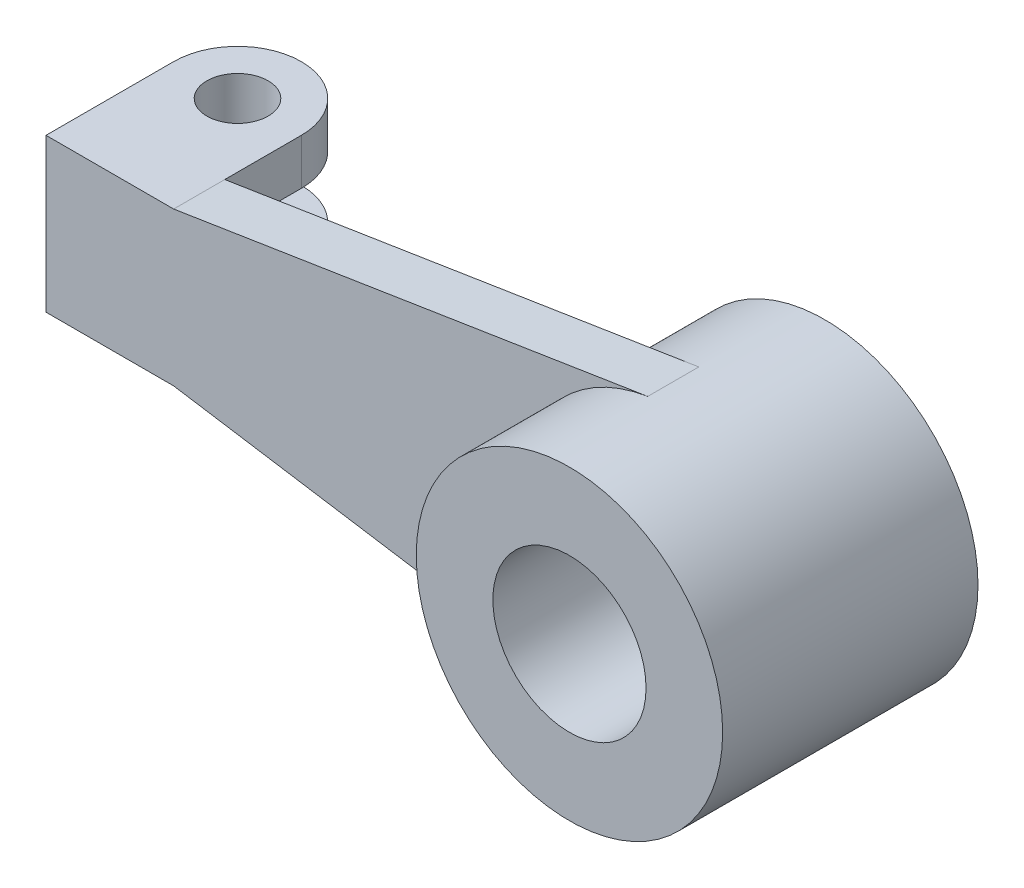
SolidWorks part; units mm, degrees
ref_plane "Front Plane" through (0, 0, 0) normal (0, 0, 1) x (1, 0, 0)
ref_plane "Top Plane" through (0, 0, 0) normal (0, 1, 0) x (1, 0, 0)
ref_plane "Right Plane" through (0, 0, 0) normal (1, 0, 0) x (0, 0, -1)
sketch "Sketch1" plane through (0, 0, 0) normal (0, 0, 1) x (1, 0, 0)
  circle A0 centre (0, 0) radius 30
  circle A1 centre (0, 0) radius 15
  dimension "D1" = 60
  dimension "D2" = 30
extrude "Boss-Extrude1" add sketch "Sketch1" along normal mid plane 50
sketch "Sketch3" plane through (0, 0, 0) normal (0, 0, 1) x (1, 0, 0)
  line L0 (0, 0) -> (-122.5, 0) construction
  line L1 (-122.5, -15) -> (-122.5, 15)
  line L2 (-122.5, 15) -> (-97.5, 15)
  line L3 (-97.5, 15) -> (-4.6717, 29.634)
  line L4 (-122.5, -15) -> (-97.5, -15)
  line L5 (-97.5, -15) -> (-4.6717, -29.634)
  circle A0 centre (0, 0) radius 30 construction
  arc A1 (-4.6717, 29.634) -> (-4.6717, -29.634) centre (0, 0) ccw
  dimension "D1" = 15
  dimension "D2" = 122.5
  dimension "D3" = 25
extrude "Boss-Extrude2" add sketch "Sketch3" along normal mid plane 10 contours A1 L5 L4 L1 L2 L3
sketch "Sketch6" plane through (-4.6717, 29.634, 0) normal (-0.1557, 0.9878, 0) x (0.9878, 0.1557, 0)
sketch "Sketch8" plane through (0, 15, 0) normal (0, 1, 0) x (1, 0, 0)
  line L0 (-122.5, 5) -> (-122.5, 20)
  line L1 (-97.5, 5) -> (-97.5, 20)
  line L2 (-122.5, 5) -> (-97.5, 5)
  line L3 (-122.5, -5) -> (-97.5, -5) construction
  arc A0 (-122.5, 20) -> (-97.5, 20) centre (-110, 20) cw
  circle A1 centre (-110, 20) radius 6
  dimension "D1" = 12
  dimension "D2" = 25
extrude "Boss-Extrude3" add sketch "Sketch8" against normal blind 9
mirror "Mirror1" about plane through (0, 0, 0) normal (0, 1, 0) of "Boss-Extrude3"
